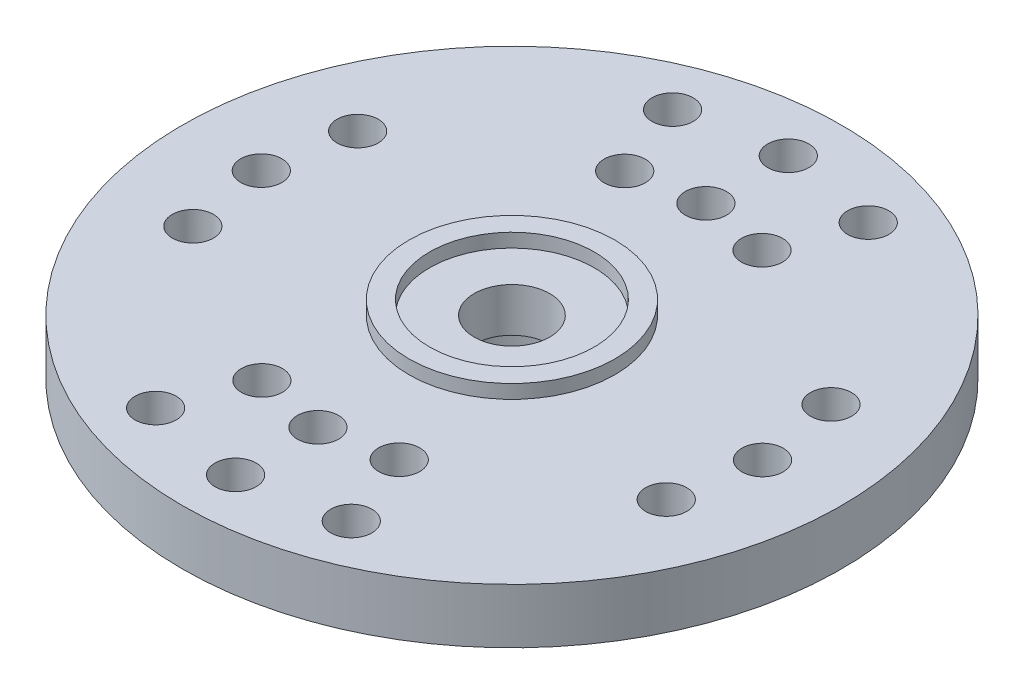
SolidWorks part; units mm, degrees
material "Delrin 2700 NC010, Low Viscosity Acetal Copolymer (SS)"
ref_plane "Front Plane" through (0, 0, 0) normal (0, 0, 1) x (1, 0, 0)
ref_plane "Top Plane" through (0, 0, 0) normal (0, 1, 0) x (1, 0, 0)
ref_plane "Right Plane" through (0, 0, 0) normal (1, 0, 0) x (0, 0, -1)
ref_plane "Plane1" through (0, 0, 0) normal (0, 0, -1) x (-1, 0, 0)
sketch "Sketch1" plane through (0, 0, 0) normal (0, 0, -1) x (-1, 0, 0)
  line L0 (-12, 0) -> (0, 0)
  line L1 (0, 0) -> (0, 2)
  line L2 (0, 2) -> (-12, 2)
  line L3 (-12, 2) -> (-12, 0)
  line L4 (0, 0) -> (0, 2) construction
revolve "Revolve1" add sketch "Sketch1" angle 360 about L4
sketch "Sketch2" plane through (0, 0, 0) normal (0, -1, 0) x (1, 0, 0)
  circle A0 centre (0, 0) radius 4.45
extrude "Boss-Extrude1" add sketch "Sketch2" along normal blind 2.6
sketch "Sketch3" plane through (0, 2, 0) normal (0, 1, 0) x (-1, 0, 0)
  circle A0 centre (0, 0) radius 3.75
extrude "Boss-Extrude2" add sketch "Sketch3" along normal blind 0.5
sketch "Sketch4" plane through (0, 0, 0) normal (0, 0, -1) x (-1, 0, 0)
  line L0 (-2.85, -2.6) -> (0, -2.6)
  line L1 (0, -2.6) -> (0, 2.5)
  line L2 (0, 2.5) -> (-3, 2.5)
  line L3 (-3, 2.5) -> (-3, 2)
  line L4 (-3, 2) -> (-1.375, 2)
  line L5 (-1.375, 2) -> (-1.375, 0.4)
  line L6 (-1.375, 0.4) -> (-2.85, 0.4)
  line L7 (-2.85, 0.4) -> (-2.85, -2.6)
  line L8 (0, -2.6) -> (0, 2.5) construction
revolve "Cut-Revolve1" cut sketch "Sketch4" angle 360 about L8
hole_wizard "Ø1.5 (1.5) Diameter Hole1" positions "Sketch6" profile "Sketch5" hole size "Ø1.5" standard "ANSI Metric"
sketch "Sketch6" plane through (0, 0, 0) normal (0, -1, 0) x (-1, 0, 0)
  point P0 (-9.125, 0)
  point P1 (9.125, 0)
  point P2 (-8.6178, -3)
  point P3 (-8.6178, 3)
  point P4 (8.6178, -3)
  point P5 (8.6178, 3)
  point P6 (0, 7.0625)
  point P7 (0, -7.0625)
  point P8 (-2.5, 6.6052)
  point P9 (2.5, 6.6052)
  point P10 (-2.5, -6.6052)
  point P11 (2.5, -6.6052)
  point P12 (0, 10.0625)
  point P13 (0, -10.0625)
  point P14 (-3.5619, 9.411)
  point P15 (3.5619, 9.411)
  point P16 (-3.5619, -9.411)
  point P17 (3.5619, -9.411)
sketch "Sketch5" plane through (9.125, 0, 0) normal (1, 0, 0) x (0, 0, -1)
  line L0 (0, 0) -> (0, 2.5)
  line L1 (0, 2.5) -> (0.75, 2.5)
  line L2 (0.75, 2.5) -> (0.75, 0)
  line L5 (0.75, 0) -> (0, 0)
  line L11 (0, -6.35) -> (0, 107.95) construction
  dimension "Thru Hole Dia." = 1.5
  dimension "Thru Hole Depth" = 2.5
